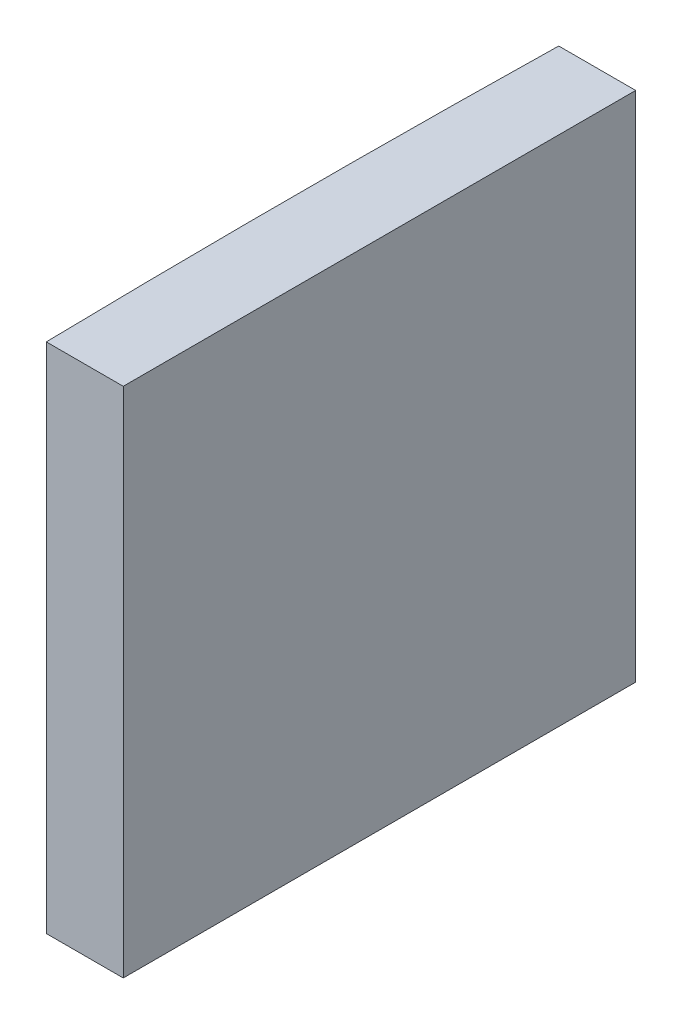
SolidWorks part; units mm, degrees
ref_plane "前视基准面" through (0, 0, 0) normal (0, 0, 1) x (1, 0, 0)
ref_plane "上视基准面" through (0, 0, 0) normal (0, 1, 0) x (1, 0, 0)
ref_plane "右视基准面" through (0, 0, 0) normal (1, 0, 0) x (0, 0, -1)
sketch "草图1" plane through (0, 0, 0) normal (0, 1, 0) x (1, 0, 0)
  line L0 (10.7432, 0) -> (-607.0701, 0) construction
  line L1 (-512.348, 10) -> (-509.3448, 10)
  line L2 (-512.348, -10) -> (-509.3448, -10)
  line L3 (-509.3448, 10) -> (-509.3448, -10)
  arc A0 (-512.348, 10) -> (-512.348, -10) centre (4.3552, 0) ccw
  point P2 (-607.0701, 0)
  point P19 (-512.4448, 0)
  point P20 (-509.3448, 0)
  dimension "D2" = 10
  dimension "D3" = 516.8
  dimension "D4" = 3.1
  dimension "D1" = 10
extrude "凸台-拉伸1" add sketch "草图1" along normal blind 20
